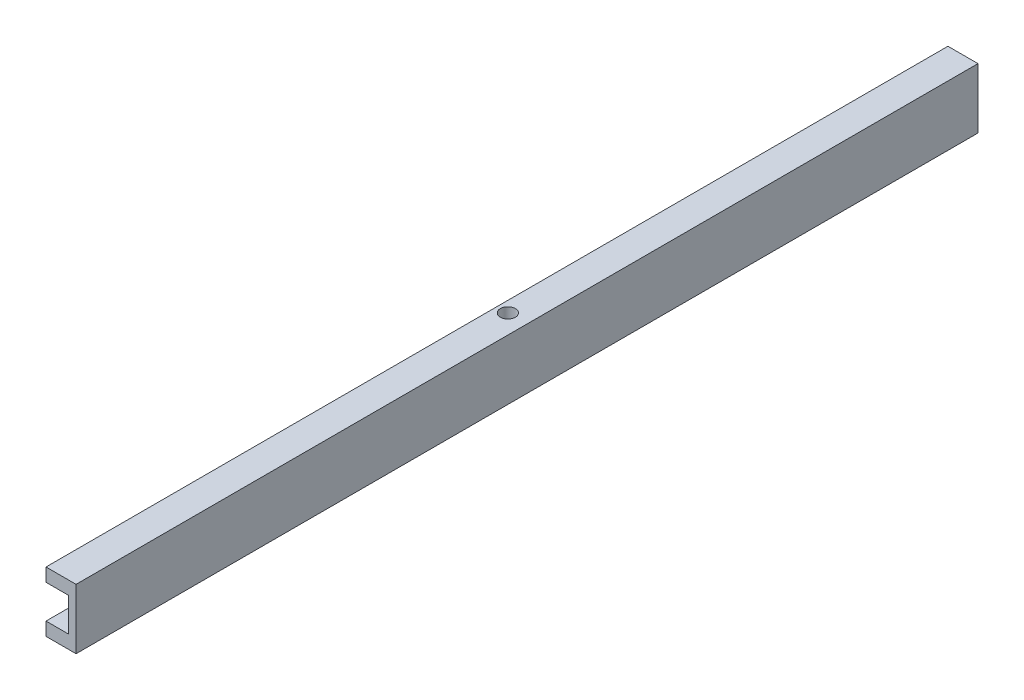
SolidWorks part; units mm, degrees
material "6061-T6 (SS)"
ref_plane "Front Plane" through (0, 0, 0) normal (0, 0, 1) x (1, 0, 0)
ref_plane "Top Plane" through (0, 0, 0) normal (0, 1, 0) x (1, 0, 0)
ref_plane "Right Plane" through (0, 0, 0) normal (1, 0, 0) x (0, 0, -1)
sketch "Sketch1" plane through (0, 0, 0) normal (0, 0, 1) x (1, 0, 0)
  line L0 (0, 19.7875) -> (9.525, 19.7875)
  line L1 (0, 0) -> (12.7, 0)
  line L2 (0, 0) -> (0, 25.4)
  line L3 (0, 25.4) -> (12.7, 25.4)
  line L4 (12.7, 0) -> (12.7, 25.4)
  line L5 (9.525, 19.7875) -> (9.525, 5.6125)
  line L6 (9.525, 5.6125) -> (0, 5.6125)
  point P7 (0, 12.7)
  dimension "D1" = 12.7
  dimension "D2" = 25.4
  dimension "D3" = 7.0875
  dimension "D4" = 7.0875
  dimension "D5" = 5.6125
  dimension "D6" = 3.175
extrude "Boss-Extrude1" add sketch "Sketch1" along normal blind 381 contours L5 L6 L2 L1 L4 L3 L0
sketch "Sketch2" plane through (0, 25.4, 0) normal (0, 1, 0) x (1, 0, 0)
  line L0 (9.525, -381) -> (9.525, 0) construction
  line L1 (9.525, -381) -> (9.525, 0)
  line L2 (4.6038, -381) -> (4.6038, 0)
  line L3 (0, -381) -> (12.7, -381) construction
  line L4 (12.7, 0) -> (0, 0)
  line L5 (0, 0) -> (0, -381)
  line L6 (0, -381) -> (12.7, -381)
  line L7 (12.7, -381) -> (12.7, 0)
  line L8 (12.7, 0) -> (0, 0)
  line L9 (0, 0) -> (0, -381)
  line L10 (0, -381) -> (12.7, -381)
  line L11 (12.7, -381) -> (12.7, 0)
  circle A29 centre (4.6038, -190.5) radius 3.175
  dimension "D3" = 190.5
  dimension "D2" = 6.35
  dimension "D1" = 0
extrude "Cut-Extrude1" cut sketch "Sketch2" against normal blind 381
